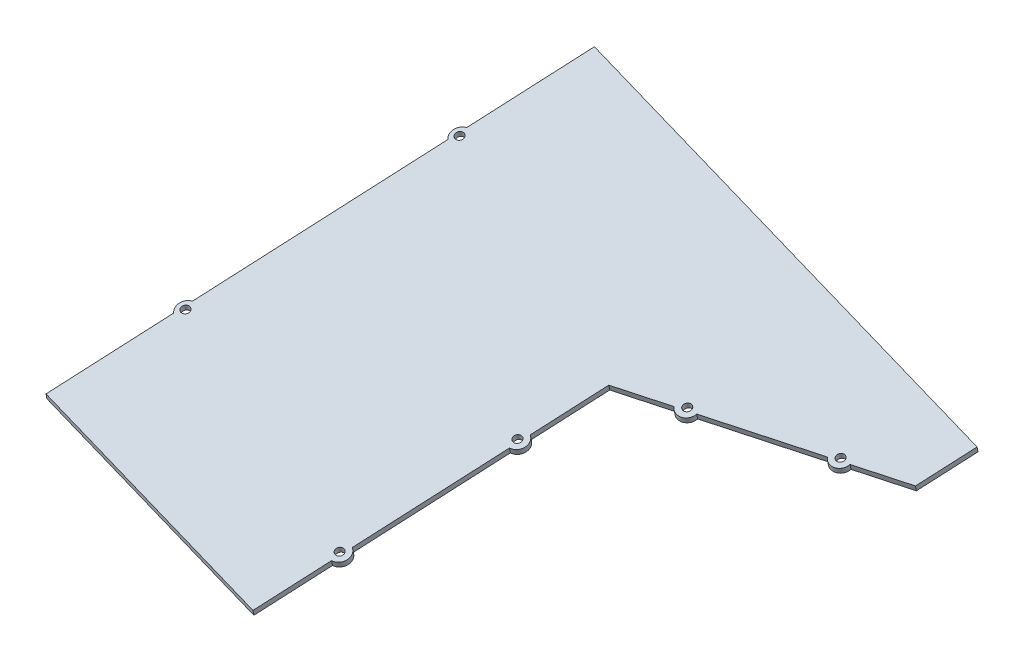
SolidWorks part; units mm, degrees
other "Markup1"
sketch "Sketch8" plane through (257.7307, 430.8513, 260.066) normal (0.119, 0.9518, 0.2826) x (0.9929, -0.114, -0.0339)
ref_plane "Front Plane" through (0, 0, 0) normal (0, 0, 1) x (1, 0, 0)
ref_plane "Top Plane" through (0, 0, 0) normal (0, 1, 0) x (1, 0, 0)
ref_plane "Right Plane" through (0, 0, 0) normal (1, 0, 0) x (0, 0, -1)
sketch "Sketch1" plane through (349.0893, 2874.0583, 804.2883) normal (-0.119, -0.9518, -0.2826) x (0.9357, -0.2027, 0.2888)
  line L8 (-227.7911, 209.5092) -> (-94.0706, 190.9665)
  line L9 (-227.7911, 209.5092) -> (-262.6002, -41.5171)
  line L10 (-94.0706, 190.9665) -> (-128.8797, -60.0598)
  line L11 (-262.6002, -41.5171) -> (-128.8797, -60.0598)
  line L14 (-222.8384, 208.8224) -> (-227.7911, 209.5092) construction
  line L16 (-257.6476, -42.2039) -> (-262.6002, -41.5171) construction
  line L20 (-131.8744, -81.6559) -> (-103.0469, 126.2339) construction
  line L21 (-265.5949, -63.1132) -> (-236.7674, 144.7766) construction
extrude "Boss-Extrude1" add sketch "Sketch1" against normal blind 3
sketch "Sketch3" plane through (688.5746, 446.8338, 894.6921) normal (0.5671, 0.368, 0.7369) x (0.5168, 0.5377, -0.6662)
  line L4 (970.9378, -219.8867) -> (970.9378, 845.2452)
  line L5 (970.9378, -219.8867) -> (-1124.2865, -289.5005)
  line L6 (970.9378, 845.2452) -> (-1124.2865, 775.6314)
  line L7 (-1124.2865, -289.5005) -> (-1124.2865, 775.6314)
extrude "Cut-Extrude2" cut sketch "Sketch3" along normal blind 80
sketch "Sketch4" plane through (357.3806, 2859.7156, 849.1036) normal (-0.119, -0.9518, -0.2826) x (0.9929, -0.1167, -0.0249)
  line L0 (-128.2348, -58.3883) -> (-111.0767, -145.7274)
  line L2 (-111.0767, -145.7274) -> (1.3739, -123.6361)
  line L3 (1.3739, -123.6361) -> (-4.114, -95.7016)
  line L5 (-4.114, -95.7016) -> (-128.2348, -58.3883)
  line L6 (-111.0767, -145.7274) -> (-159.9298, 102.9476) construction
  line L7 (-106.8738, -167.1212) -> (-147.332, 38.8213) construction
  line L10 (-0.4283, -114.4625) -> (-0.8018, -112.5614) construction
extrude "Boss-Extrude2" add sketch "Sketch4" against normal blind 3
sketch "Sketch6" plane through (357.7375, 2862.5711, 849.9514) normal (0.119, 0.9518, 0.2826) x (0.9929, -0.114, -0.0339)
  line L0 (-239.4883, 173.504) -> (-290.652, -74.7059) construction
  line L1 (-241.9369, 174.0087) -> (2.5236, 123.6179) construction
  line L2 (-160.8803, -101.4558) -> (-293.1005, -74.2012) construction
  line L3 (-232.6381, 194.3531) -> (-275.0098, -11.2043) construction
  line L4 (-237.5352, 195.3625) -> (-279.9068, -10.1949) construction
  line L5 (-241.9369, 174.0087) -> (-267.5187, 49.9038) construction
  line L6 (-293.1005, -74.2012) -> (-241.9369, 174.0087) construction
  line L7 (-254.7278, 111.9562) -> (-39.066, 67.5018) construction
  line L8 (-267.5187, 49.9038) -> (-42.6515, 3.5518) construction
  line L9 (-280.3096, -12.1487) -> (-64.6478, -56.6032) construction
  line L10 (-127.6862, 59.5783) -> (-144.2833, -20.9387) construction
  line L11 (-127.6862, 59.5783) -> (-65.455, 77.657) construction
  line L12 (-135.9847, 19.3198) -> (58.7409, -20.8191) construction
  line L13 (-127.6862, 59.5783) -> (-160.8803, -101.4558) construction
  line L14 (-144.2833, -20.9387) -> (55.9608, -62.2152) construction
  line L15 (-152.5818, -61.1973) -> (42.1439, -101.3362) construction
  line L16 (-96.5706, 68.6177) -> (-70.701, -20.4315) construction
  line L17 (-3.2237, 95.7358) -> (-127.6862, 59.5783) construction
  line L18 (-65.455, 77.657) -> (-43.2641, 1.2706) construction
  line L19 (-34.3394, 86.6964) -> (-8.4698, -2.3528) construction
  circle A0 centre (-252.2793, 111.4515) radius 5
  circle A2 centre (-137.4539, 19.6226) radius 5
  circle A3 centre (-154.0509, -60.8944) radius 5
  circle A4 centre (-96.9891, 70.0581) radius 5
  circle A5 centre (-34.7578, 88.1369) radius 5
  circle A6 centre (-277.8611, -12.6534) radius 5
  point P14 (-254.7278, 111.9562)
  point P15 (-144.2833, -20.9387)
  point P26 (-280.3096, -12.1487)
  dimension "D1" = 10
  dimension "D3" = 10
  dimension "D5" = 10
  dimension "D4" = 1.5
  dimension "D6" = 1.5
extrude "Boss-Extrude3" add sketch "Sketch6" against normal blind 3
sketch "Sketch7" plane through (357.7375, 2862.5711, 849.9514) normal (0.119, 0.9518, 0.2826) x (0.9929, -0.114, -0.0339)
  line L0 (-279.4354, -7.9077) -> (-255.602, 107.7153) construction
  line L1 (-253.8536, 116.1972) -> (-255.602, 107.7153) construction
  line L2 (-253.8536, 116.1972) -> (-241.9369, 174.0087) construction
  line L3 (-254.7278, 111.9562) -> (-253.2587, 111.6534) construction
  line L4 (-279.4354, -7.9077) -> (-281.1838, -16.3897) construction
  line L5 (-280.3096, -12.1487) -> (-278.8405, -12.4515) construction
  line L6 (-293.1005, -74.2012) -> (-281.1838, -16.3897) construction
  line L7 (-29.759, 88.027) -> (-38.9197, 85.3658) construction
  line L8 (-34.3394, 86.6964) -> (-34.7578, 88.1369) construction
  line L10 (-38.9197, 85.3658) -> (-91.9903, 69.9483) construction
  line L11 (-91.9903, 69.9483) -> (-101.1509, 67.2871) construction
  line L12 (-96.5706, 68.6177) -> (-96.9891, 70.0581) construction
  line L13 (-101.1509, 67.2871) -> (-127.6862, 59.5783) construction
  line L14 (-135.0218, 23.9913) -> (-136.9477, 14.6483) construction
  line L15 (-135.9847, 19.3198) -> (-137.4539, 19.6226) construction
  line L16 (-136.9477, 14.6483) -> (-151.6188, -56.5258) construction
  line L17 (-151.6188, -56.5258) -> (-153.5447, -65.8688) construction
  line L18 (-152.5818, -61.1973) -> (-154.0509, -60.8944) construction
  line L19 (-153.5447, -65.8688) -> (-160.8803, -101.4558) construction
  circle A0 centre (-253.2587, 111.6534) radius 2.1
  circle A1 centre (-278.8405, -12.4515) radius 2.1
  circle A2 centre (-34.7578, 88.1369) radius 2.1
  circle A3 centre (-96.9891, 70.0581) radius 2.1
  circle A4 centre (-137.4539, 19.6226) radius 2.1
  circle A5 centre (-154.0509, -60.8944) radius 2.1
  dimension "D1" = 4.2
  dimension "D3" = 4.2
  dimension "D5" = 4.2
  dimension "D7" = 4.2
  dimension "D9" = 4.2
  dimension "D11" = 4.2
  dimension "D2" = 1.5
  dimension "D4" = 1.5
  dimension "D6" = 1.5
  dimension "D8" = 1.5
  dimension "D10" = 1.5
  dimension "D12" = 1.5
extrude "Cut-Extrude8" cut sketch "Sketch7" against normal through all both and the other way through all
